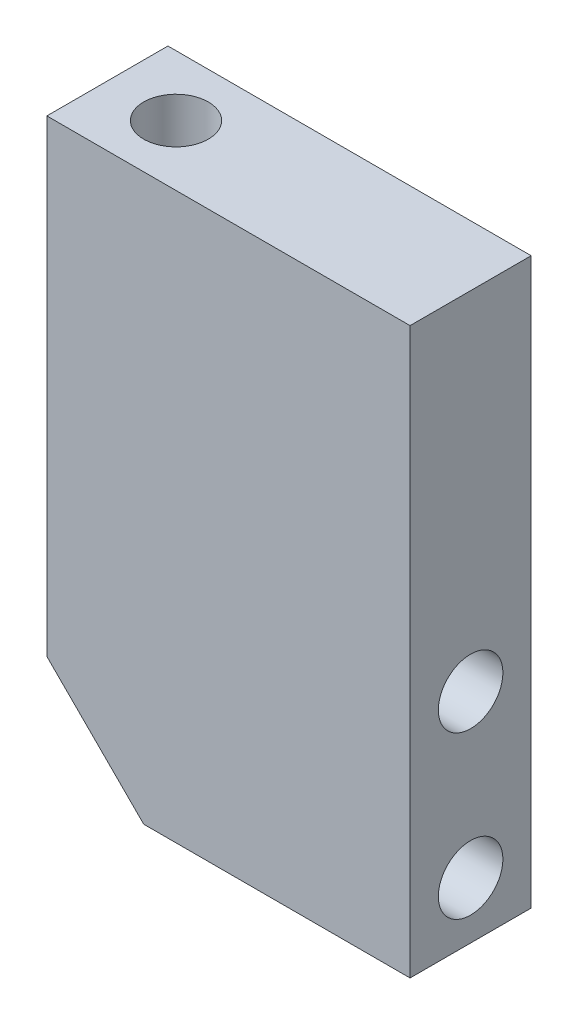
SolidWorks part; units mm, degrees
ref_plane "Płaszczyzna przednia" through (0, 0, 0) normal (0, 0, 1) x (1, 0, 0)
ref_plane "Płaszczyzna górna" through (0, 0, 0) normal (0, 1, 0) x (1, 0, 0)
ref_plane "Płaszczyzna prawa" through (0, 0, 0) normal (1, 0, 0) x (0, 0, -1)
sketch "Szkic1" plane through (0, 0, 0) normal (0, 0, 1) x (1, 0, 0)
  line L1 (22.5, -35) -> (-22.5, -35)
  line L2 (22.5, -35) -> (22.5, 35)
  line L3 (22.5, 35) -> (-22.5, 35)
  line L4 (-22.5, -35) -> (-22.5, 35)
  line L5 (22.5, -35) -> (-22.5, 35) construction
  line L6 (22.5, 35) -> (-22.5, -35) construction
  point P0 (0, 0)
  dimension "D1" = 45
  dimension "D2" = 70
extrude "Dodanie-wyciągnięcie1" add sketch "Szkic1" along normal blind 15
sketch "Szkic3" plane through (0, 35, 0) normal (0, 1, 0) x (1, 0, 0)
  line L1 (-22.5, -15) -> (-22.5, 0) construction
  line L2 (22.5, 0) -> (-22.5, 0) construction
  circle A1 centre (-14, -7.5) radius 4
  dimension "D1" = 8.5
  dimension "D4" = 8
  dimension "D3" = 7.5
extrude "Wytnij-wyciągnięcie1" cut sketch "Szkic3" against normal blind 15
chamfer "Sfazowanie1" distance 12 angle 45 1 edges at (-22.5, -35, 7.5)
sketch "Szkic4" plane through (22.5, 0, 0) normal (1, 0, 0) x (0, 0, -1)
  line L0 (-15, -35) -> (0, -35) construction
  line L1 (-15, -35) -> (-15, 35) construction
  circle A0 centre (-7.5, -28) radius 4
  circle A1 centre (-7.5, -8) radius 4
  dimension "D1" = 8
  dimension "D2" = 8
  dimension "D3" = 7
  dimension "D4" = 7.5
  dimension "D5" = 20
extrude "Wytnij-wyciągnięcie2" cut sketch "Szkic4" against normal blind 25
